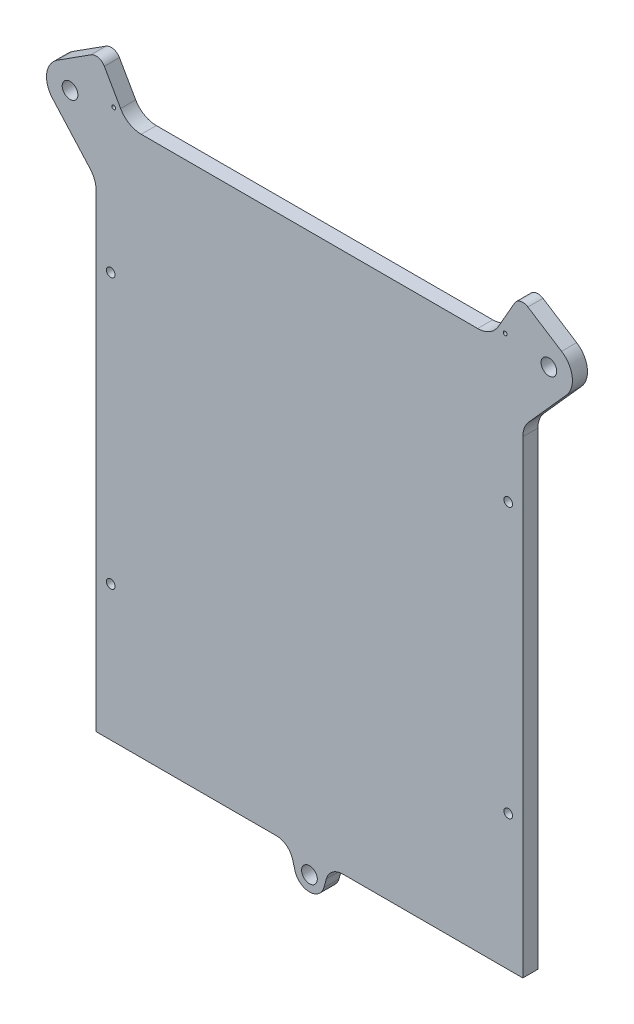
SolidWorks part; units mm, degrees
material "6061-T6 (SS)"
ref_plane "Front Plane" through (0, 0, 0) normal (0, 0, 1) x (1, 0, 0)
ref_plane "Top Plane" through (0, 0, 0) normal (0, 1, 0) x (1, 0, 0)
ref_plane "Right Plane" through (0, 0, 0) normal (1, 0, 0) x (0, 0, -1)
sketch "Sketch1" plane through (0, 0, 0) normal (0, 0, 1) x (1, 0, 0)
  line L0 (-89.8724, 56.9024) -> (89.8724, 56.9024) construction
  line L1 (-89.8724, 113.7286) -> (89.8724, 113.7286)
  line L2 (-89.8724, 113.7286) -> (-89.8724, -113.7286)
  line L3 (-89.8724, -113.7286) -> (89.8724, -113.7286)
  line L4 (89.8724, 113.7286) -> (89.8724, -113.7286) construction
  line L5 (89.8724, -56.75) -> (-89.8724, -56.75) construction
  line L6 (-83.72, 56.9024) -> (-83.72, -56.75) construction
  line L7 (-108.2601, 108.1294) -> (-92.4145, 90.3905)
  line L8 (-106.2114, 123.0727) -> (-92.0283, 132.1479)
  line L9 (-89.8724, 0) -> (89.8724, 0) construction
  line L10 (0, 113.7286) -> (0, -113.7286)
  line L11 (-86.3982, 130.7609) -> (-79.558, 118.7728)
  line L12 (-6.0681, -122.6796) -> (-7.1217, -118.9209)
  line L13 (6.0681, -122.6796) -> (7.1217, -118.9209)
  line L14 (0, -113.7286) -> (0, -127.2806)
  circle A0 centre (-83.72, 56.9024) radius 1.8288
  circle A1 centre (-100.8724, 114.7286) radius 3.302
  arc A2 (-92.0283, 132.1479) -> (-86.3982, 130.7609) centre (-89.8724, 128.7786) cw
  arc A3 (-79.558, 118.7728) -> (-70.8724, 113.7286) centre (-70.8724, 123.7286) ccw
  arc A4 (-106.2114, 123.0727) -> (-108.2601, 108.1294) centre (-100.8724, 114.7286) ccw
  arc A5 (-92.4145, 90.3905) -> (-89.8724, 83.7286) centre (-99.8724, 83.7286) cw
  circle A6 centre (0, -120.9786) radius 3.302
  arc A7 (-6.0681, -122.6796) -> (6.0681, -122.6796) centre (0, -120.9786) ccw
  circle A8 centre (-82.4526, 117.7286) radius 0.8
  circle A9 centre (-83.72, -56.75) radius 1.8288
  arc A10 (-7.1217, -118.9209) -> (-13.9698, -113.7286) centre (-13.9698, -120.8406) ccw
  arc A11 (7.1217, -118.9209) -> (13.9698, -113.7286) centre (13.9698, -120.8406) cw
  point P8 (0, 0)
  point P18 (-89.8724, 132.7786)
  dimension "D5" = 6.604
  dimension "D6" = 3.6576
  dimension "D7" = 6.604
  dimension "D3" = 56.8262
  dimension "D8" = 83.72
  dimension "D13" = 3.6576
  dimension "D10" = 11
  dimension "D11" = 19
  dimension "D12" = 30
  dimension "D14" = 4
  dimension "D15" = 19.05
  dimension "D9" = 19.05
  dimension "D17" = 10
  dimension "D18" = 10
  dimension "D19" = 6.604
  dimension "D21" = 3
  dimension "D24" = 1.6
  dimension "D25" = 7.112
  dimension "D27" = 7.112
  dimension "D1" = 179.7448
  dimension "D2" = 227.4572
  dimension "D4" = 113.6524
  dimension "D16" = 1
  dimension "D20" = 7.25
  dimension "D22" = 4
  dimension "D23" = 7.4198
  dimension "D26" = 13.9698
  dimension "D28" = 13.9698
extrude "Plate" add sketch "Sketch1" against normal blind 6.35
mirror "Plate Mirror" about plane through (0, 0, 0) normal (1, 0, 0) of "Plate"
sketch "Sketch2" plane through (0, 0, -6.35) normal (0, 0, 1) x (1, 0, 0)
  line L0 (-83.72, 56.9024) -> (83.72, -56.75) construction
  line L1 (-83.72, 56.9024) -> (83.72, 56.9024) construction
  line L2 (-100.8724, 114.7286) -> (0, 56.9024) construction
  line L3 (0, 0) -> (-83.72, 0) construction
  line L4 (-83.72, 0) -> (-83.72, 104.8958) construction
  line L5 (-83.72, 104.8958) -> (0, 104.8958) construction
  line L6 (0, 104.8958) -> (0, 0) construction
  line L7 (-79.166, 106.8958) -> (-4, 106.8958)
  line L8 (-4, 106.8958) -> (-4, 63.8061)
  line L9 (-4, 63.8061) -> (-79.166, 106.8958)
  line L10 (-75.72, 95.6991) -> (-75.72, 64.9024)
  line L11 (-75.72, 64.9024) -> (-21.9981, 64.9024)
  line L12 (0, 0) -> (-83.72, -56.75) construction
  line L13 (-21.9981, 64.9024) -> (-75.72, 95.6991)
  line L14 (-71.3228, 53.0924) -> (-4, 7.396)
  line L15 (-4, 7.396) -> (-4, 53.0924)
  line L16 (-4, 53.0924) -> (-71.3228, 53.0924)
  line L17 (-79.91, 49.7115) -> (-79.91, 3.81)
  line L18 (-79.91, 3.81) -> (-12.2849, 3.81)
  line L19 (-12.2849, 3.81) -> (-79.91, 49.7115)
  line L20 (-83.72, -56.75) -> (0, -120.9786) construction
  line L21 (0, -120.9786) -> (0, 0) construction
  line L22 (-83.72, -56.75) -> (83.72, -56.75) construction
  line L23 (-83.72, 0) -> (-83.72, -56.75) construction
  line L24 (-12.411, -3.81) -> (-79.91, -3.81)
  line L25 (-79.91, -3.81) -> (-79.91, -49.5645)
  line L26 (-79.91, -49.5645) -> (-12.411, -3.81)
  line L27 (-4, -7.3143) -> (-4, -52.75)
  line L28 (-4, -52.75) -> (-71.0287, -52.75)
  line L29 (-71.0287, -52.75) -> (-4, -7.3143)
  line L31 (-4, -60.75) -> (-4, -110.3476)
  line L32 (-4, -110.3476) -> (-68.6489, -60.75)
  line L33 (-68.6489, -60.75) -> (-4, -60.75)
  line L34 (-79.72, -62.3395) -> (-23.1637, -105.7286)
  line L35 (-23.1637, -105.7286) -> (-79.72, -105.7286)
  line L36 (-79.72, -105.7286) -> (-79.72, -62.3395)
  line L37 (-83.72, -56.75) -> (-83.72, -109.7286) construction
  line L38 (-83.72, -109.7286) -> (-14.664, -109.7286) construction
  line L39 (-89.8724, -113.7286) -> (-13.9698, -113.7286) construction
  dimension "D1" = 8
  dimension "D2" = 8
  dimension "D3" = 4
  dimension "D4" = 4
  dimension "D5" = 4
  dimension "D6" = 4
  dimension "D12" = 2
  dimension "D16" = 4
  dimension "D17" = 4
  dimension "D18" = 6
  dimension "D19" = 2
  dimension "D20" = 4
  dimension "D21" = 4
  dimension "D22" = 4
extrude "Weight Saving Cuts" cut sketch "Sketch2" along normal blind 3.81 contours L28 L29 L27 | L32 L33 L31 | L35 L36 L34 | L26 L25 L24 | L19 L18 L17 | L16 L15 L14 | L13 L11 L10 | L8 L9 L7
fillet "Weight Saving Cut Fillets" radius 7.112 24 edges at (-4, 106.8958, -4.445) (-4, -52.75, -4.445) (-4, -110.3476, -4.445) (-23.1637, -105.7286, -4.445) (-68.6489, -60.75, -4.445) (-79.72, -105.7286, -4.445) (-71.0287, -52.75, -4.445) (-4, -60.75, -4.445) (-4, -7.3143, -4.445) (-79.72, -62.3395, -4.445) (-79.91, -3.81, -4.445) (-12.411, -3.81, -4.445) (-79.91, -49.5645, -4.445) (-79.91, 3.81, -4.445) (-79.91, 49.7115, -4.445) (-12.2849, 3.81, -4.445) (-4, 7.396, -4.445) (-4, 53.0924, -4.445) (-71.3228, 53.0924, -4.445) (-75.72, 95.6991, -4.445) (-75.72, 64.9024, -4.445) (-21.9981, 64.9024, -4.445) (-4, 63.8061, -4.445) (-79.166, 106.8958, -4.445)
mirror "Weight Saving Mirror" about plane through (0, 0, 0) normal (1, 0, 0) of "Weight Saving Cut Fillets", "Weight Saving Cuts"
sketch "Sketch3" plane through (0, 0, -6.35) normal (0, 0, -1) x (-1, 0, 0)
  line L20 (6.0681, -122.6796) -> (7.1217, -118.9209) construction
  line L27 (-6.0681, -122.6796) -> (-7.1217, -118.9209) construction
  line L28 (6.0681, -122.6796) -> (7.1217, -118.9209)
  line L29 (-6.0681, -122.6796) -> (-7.1217, -118.9209)
  line L30 (-13.9698, -113.7286) -> (13.9698, -113.7286)
  circle A0 centre (83.72, -56.75) radius 4.7625
  circle A1 centre (83.72, 56.9024) radius 4.7625
  circle A2 centre (-83.72, 56.9024) radius 4.7625
  circle A3 centre (-83.72, -56.75) radius 4.7625
  circle A4 centre (-100.8724, 114.7286) radius 9.906
  circle A5 centre (100.8724, 114.7286) radius 9.906
  arc A6 (-6.0681, -122.6796) -> (6.0681, -122.6796) centre (0, -120.9786) ccw construction
  arc A7 (-106.2114, 123.0727) -> (-108.2601, 108.1294) centre (-100.8724, 114.7286) ccw construction
  arc A8 (108.2601, 108.1294) -> (106.2114, 123.0727) centre (100.8724, 114.7286) ccw construction
  arc A9 (-7.1217, -118.9209) -> (-13.9698, -113.7286) centre (-13.9698, -120.8406) ccw construction
  arc A10 (13.9698, -113.7286) -> (7.1217, -118.9209) centre (13.9698, -120.8406) ccw construction
  arc A11 (-6.0681, -122.6796) -> (6.0681, -122.6796) centre (0, -120.9786) ccw
  arc A12 (-7.1217, -118.9209) -> (-13.9698, -113.7286) centre (-13.9698, -120.8406) ccw
  arc A13 (13.9698, -113.7286) -> (7.1217, -118.9209) centre (13.9698, -120.8406) ccw
  dimension "D1" = 9.525
  dimension "D2" = 9.525
  dimension "D3" = 9.525
  dimension "D4" = 9.525
split line "Simulation Split Line" [suppressed]
sketch "Sketch4" plane through (0, 0, 0) normal (0, 0, 1) x (1, 0, 0)
  line L0 (-89.8724, -113.7286) -> (-13.9698, -113.7286) construction
  line L1 (-78, 97.7714) -> (78, 97.7714)
  line L2 (-78, 97.7714) -> (-78, -107.7286)
  line L3 (-78, -107.7286) -> (78, -107.7286)
  line L4 (78, 97.7714) -> (78, -107.7286)
  point P4 (0, 97.7714)
  dimension "D1" = 6
  dimension "D2" = 205.5
  dimension "D3" = 156
split line "Split Line1" [suppressed]
sketch "CAM Sides" [suppressed] plane through (0, 0, 0) normal (0, 0, 1) x (1, 0, 0)
  line L0 (89.8724, -113.7286) -> (15.6944, -113.7286) construction
  line L1 (89.8724, 83.7286) -> (140.6724, 83.7286)
  line L2 (89.8724, 83.7286) -> (89.8724, -151.8286)
  line L5 (-89.8724, 83.7286) -> (-140.6724, 83.7286)
  line L6 (-89.8724, 83.7286) -> (-89.8724, -151.8286)
  dimension "D1" = 38.1
  dimension "D2" = 50.8
sketch "CAM Top" [suppressed] plane through (0, 0, 0) normal (0, 0, 1) x (1, 0, 0)
  line L0 (89.8724, 83.7286) -> (89.8724, 71.0286)
  line L1 (89.8724, 83.7286) -> (89.8724, -113.7286) construction
  line L2 (-89.8724, 83.7286) -> (-89.8724, 71.0286)
  line L3 (-89.8724, 83.7286) -> (-89.8724, -113.7286) construction
  line L17 (5.8573, -123.3041) -> (7.4318, -119.3382)
  line L18 (15.6944, -113.7286) -> (89.8724, -113.7286)
  line L19 (89.8724, -113.7286) -> (89.8724, 83.7286)
  line L20 (92.4145, 90.3905) -> (108.2601, 108.1294)
  line L21 (106.2114, 123.0727) -> (92.0283, 132.1479)
  line L22 (86.3982, 130.7609) -> (79.558, 118.7728)
  line L23 (70.8724, 113.7286) -> (-70.8724, 113.7286)
  line L24 (-79.558, 118.7728) -> (-86.3982, 130.7609)
  line L25 (-92.0283, 132.1479) -> (-106.2114, 123.0727)
  line L26 (-108.2601, 108.1294) -> (-92.4145, 90.3905)
  line L27 (-89.8724, 83.7286) -> (-89.8724, -113.7286)
  line L28 (-89.8724, -113.7286) -> (-15.6944, -113.7286)
  line L29 (-7.4318, -119.3382) -> (-5.8573, -123.3041)
  line L33 (92.4145, 90.3905) -> (108.2601, 108.1294)
  line L34 (106.2114, 123.0727) -> (92.0283, 132.1479)
  line L35 (86.3982, 130.7609) -> (79.558, 118.7728)
  line L36 (70.8724, 113.7286) -> (-70.8724, 113.7286)
  line L37 (-79.558, 118.7728) -> (-86.3982, 130.7609)
  line L38 (-92.0283, 132.1479) -> (-106.2114, 123.0727)
  line L39 (-108.2601, 108.1294) -> (-92.4145, 90.3905)
  arc A9 (-5.8573, -123.3041) -> (5.8573, -123.3041) centre (0, -120.9786) ccw
  arc A10 (92.4145, 90.3905) -> (89.8724, 83.7286) centre (99.8724, 83.7286) ccw
  arc A11 (108.2601, 108.1294) -> (106.2114, 123.0727) centre (100.8724, 114.7286) ccw
  arc A12 (92.0283, 132.1479) -> (86.3982, 130.7609) centre (89.8724, 128.7786) ccw
  arc A13 (70.8724, 113.7286) -> (79.558, 118.7728) centre (70.8724, 123.7286) ccw
  arc A14 (-79.558, 118.7728) -> (-70.8724, 113.7286) centre (-70.8724, 123.7286) ccw
  arc A15 (-86.3982, 130.7609) -> (-92.0283, 132.1479) centre (-89.8724, 128.7786) ccw
  arc A16 (-106.2114, 123.0727) -> (-108.2601, 108.1294) centre (-100.8724, 114.7286) ccw
  arc A17 (-89.8724, 83.7286) -> (-92.4145, 90.3905) centre (-99.8724, 83.7286) ccw
  arc A19 (92.4145, 90.3905) -> (89.8724, 83.7286) centre (99.8724, 83.7286) ccw
  arc A20 (108.2601, 108.1294) -> (106.2114, 123.0727) centre (100.8724, 114.7286) ccw
  arc A21 (92.0283, 132.1479) -> (86.3982, 130.7609) centre (89.8724, 128.7786) ccw
  arc A22 (70.8724, 113.7286) -> (79.558, 118.7728) centre (70.8724, 123.7286) ccw
  arc A23 (-79.558, 118.7728) -> (-70.8724, 113.7286) centre (-70.8724, 123.7286) ccw
  arc A24 (-86.3982, 130.7609) -> (-92.0283, 132.1479) centre (-89.8724, 128.7786) ccw
  arc A25 (-106.2114, 123.0727) -> (-108.2601, 108.1294) centre (-100.8724, 114.7286) ccw
  arc A26 (-89.8724, 83.7286) -> (-92.4145, 90.3905) centre (-99.8724, 83.7286) ccw
  arc A28 (15.6944, -113.7286) -> (7.4318, -119.3382) centre (15.6944, -122.6186) ccw
  arc A30 (-7.4318, -119.3382) -> (-15.6944, -113.7286) centre (-15.6944, -122.6186) ccw
  dimension "D1" = 12.7
  dimension "D2" = 0
sketch "Sketch5" plane through (0, 0, -6.35) normal (0, 0, -1) x (-1, 0, 0)
  line L1 (-110.7784, 132.7786) -> (110.7784, 132.7786)
  line L2 (-110.7784, 132.7786) -> (-110.7784, -127.2806)
  line L3 (-110.7784, -127.2806) -> (110.7784, -127.2806)
  line L4 (110.7784, 132.7786) -> (110.7784, -127.2806)
  arc A1 (-6.0681, -122.6796) -> (6.0681, -122.6796) centre (0, -120.9786) ccw construction
  arc A2 (-106.2114, 123.0727) -> (-108.2601, 108.1294) centre (-100.8724, 114.7286) ccw construction
  arc A3 (-86.3982, 130.7609) -> (-92.0283, 132.1479) centre (-89.8724, 128.7786) ccw construction
  arc A4 (108.2601, 108.1294) -> (106.2114, 123.0727) centre (100.8724, 114.7286) ccw construction
